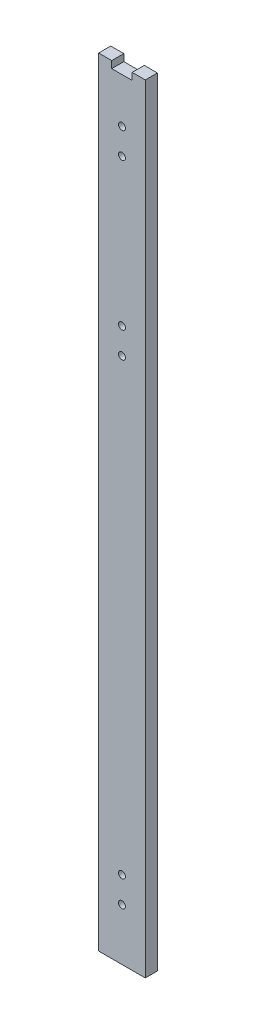
SolidWorks part; units mm, degrees
ref_plane "Front" through (0, 0, 0) normal (0, 0, 1) x (1, 0, 0)
ref_plane "Top" through (0, 0, 0) normal (0, 1, 0) x (1, 0, 0)
ref_plane "Right" through (0, 0, 0) normal (1, 0, 0) x (0, 0, -1)
sketch "草图1" plane through (0, 0, 0) normal (0, 1, 0) x (1, 0, 0)
  line L1 (13.5, -3.5) -> (-13.5, -3.5)
  line L2 (13.5, -3.5) -> (13.5, 3.5)
  line L3 (13.5, 3.5) -> (-13.5, 3.5)
  line L4 (-13.5, -3.5) -> (-13.5, 3.5)
  line L5 (13.5, -3.5) -> (-13.5, 3.5) construction
  line L6 (13.5, 3.5) -> (-13.5, -3.5) construction
  point P0 (0, 0)
  dimension "D1" = 7
  dimension "D2" = 27
extrude "凸台-拉伸1" add sketch "草图1" along normal blind 450
sketch "草图2" plane through (0, 0, -3.5) normal (0, 0, -1) x (-1, 0, 0)
  line L0 (-13.5, 450) -> (13.5, 450) construction
  line L1 (-5.914, 445.959) -> (5.914, 445.959)
  line L2 (-5.914, 445.959) -> (-5.914, 454.041)
  line L3 (-5.914, 454.041) -> (5.914, 454.041)
  line L4 (5.914, 445.959) -> (5.914, 454.041)
  line L5 (-5.914, 445.959) -> (5.914, 454.041) construction
  line L6 (-5.914, 454.041) -> (5.914, 445.959) construction
  point P0 (0, 450)
extrude "切除-拉伸1" cut sketch "草图2" against normal through all
sketch "草图3" plane through (0, 0, -3.5) normal (0, 0, -1) x (-1, 0, 0)
  line L0 (0, 445.959) -> (0, 0) construction
  line L1 (-5.914, 445.959) -> (5.914, 445.959) construction
  line L2 (-13.5, 0) -> (13.5, 0) construction
  line L3 (5.914, 450) -> (13.5, 450) construction
  line L4 (-13.5, 450) -> (-5.914, 450) construction
  circle A0 centre (0, 420) radius 2
  circle A1 centre (0, 405) radius 2
  circle A2 centre (0, 320) radius 2
  circle A3 centre (0, 305) radius 2
  circle A4 centre (0, 30) radius 2
  circle A5 centre (0, 45) radius 2
  dimension "D1" = 4
  dimension "D2" = 4
  dimension "D5" = 4
  dimension "D6" = 4
  dimension "D9" = 4
  dimension "D10" = 4
  dimension "D3" = 30
  dimension "D4" = 45
  dimension "D7" = 130
  dimension "D8" = 145
  dimension "D11" = 30
  dimension "D12" = 45
extrude "切除-拉伸2" cut sketch "草图3" against normal through all
